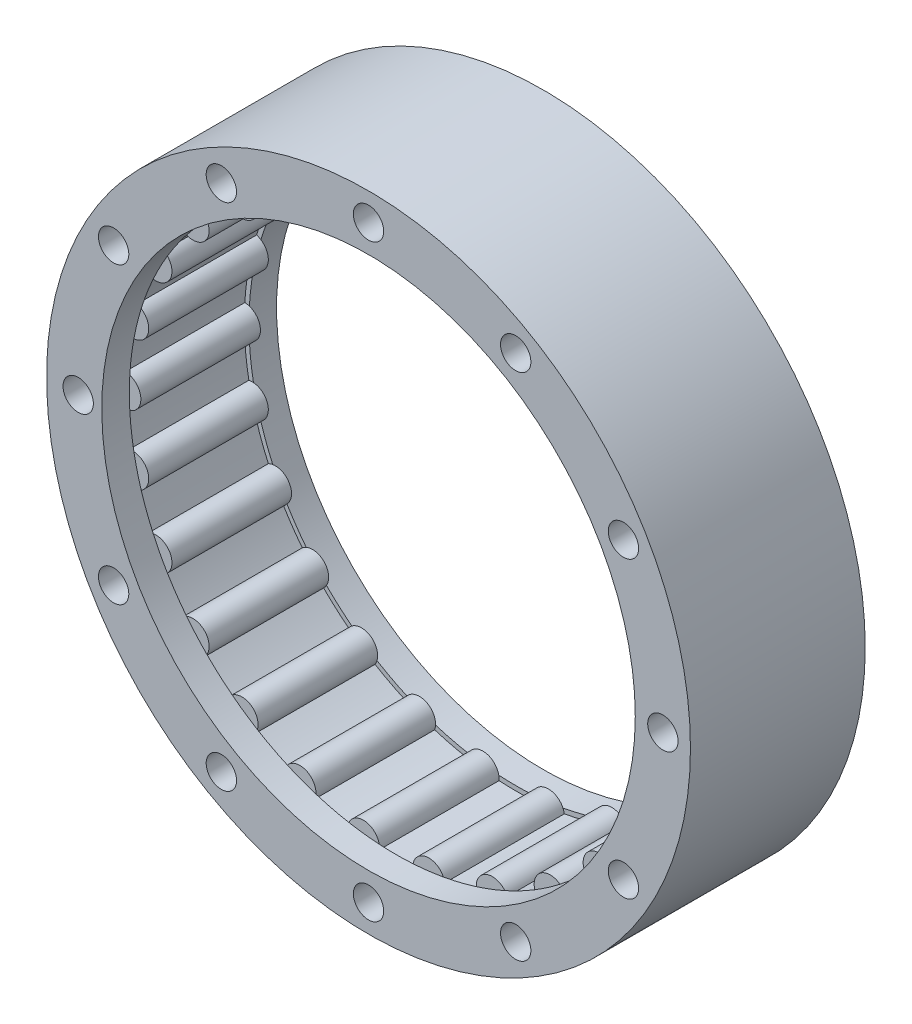
SolidWorks part; units mm, degrees
ref_plane "前视基准面" through (0, 0, 0) normal (0, 0, 1) x (1, 0, 0)
ref_plane "上视基准面" through (0, 0, 0) normal (0, 1, 0) x (1, 0, 0)
ref_plane "右视基准面" through (0, 0, 0) normal (1, 0, 0) x (0, 0, -1)
other "Configuration Table"
sketch "草图1" plane through (0, 0, 0) normal (0, 0, 1) x (1, 0, 0)
  line L0 (0, 0) -> (29.5, 0) construction
  circle A0 centre (0, 0) radius 35
  circle A1 centre (29.5, 0) radius 1.6 construction
  circle A2 centre (0, 0) radius 29.5
  dimension "D1" = 70
  dimension "D2" = 3.2
  dimension "D4" = 59
  dimension "D3" = 29.5
extrude "凸台-拉伸1" add sketch "草图1" along normal blind 13
sketch "草图2" plane through (0, 0, 13) normal (0, 0, 1) x (1, 0, 0)
  circle A0 centre (29.5, 0) radius 1.75
  circle A1 centre (28.6428, -7.0598) radius 1.75
  circle A2 centre (26.121, -13.7093) radius 1.75
  circle A3 centre (22.0811, -19.5621) radius 1.75
  circle A4 centre (16.7579, -24.278) radius 1.75
  circle A5 centre (10.4608, -27.583) radius 1.75
  circle A6 centre (3.5558, -29.2849) radius 1.75
  circle A7 centre (-3.5558, -29.2849) radius 1.75
  circle A8 centre (-10.4608, -27.583) radius 1.75
  circle A9 centre (-16.7579, -24.278) radius 1.75
  circle A10 centre (-22.0811, -19.5621) radius 1.75
  circle A11 centre (-26.121, -13.7093) radius 1.75
  circle A12 centre (-28.6428, -7.0598) radius 1.75
  circle A13 centre (-29.5, 0) radius 1.75
  circle A14 centre (-28.6428, 7.0598) radius 1.75
  circle A15 centre (-26.121, 13.7093) radius 1.75
  circle A16 centre (-22.0811, 19.5621) radius 1.75
  circle A17 centre (-16.7579, 24.278) radius 1.75
  circle A18 centre (-10.4608, 27.583) radius 1.75
  circle A19 centre (-3.5558, 29.2849) radius 1.75
  circle A20 centre (3.5558, 29.2849) radius 1.75
  circle A21 centre (10.4608, 27.583) radius 1.75
  circle A22 centre (16.7579, 24.278) radius 1.75
  circle A23 centre (22.0811, 19.5621) radius 1.75
  circle A24 centre (26.121, 13.7093) radius 1.75
  circle A25 centre (28.6428, 7.0598) radius 1.75
  point P50 (0, 0)
  dimension "D2" = 3.5
  dimension "D1" = 29.5
  dimension "D3" = 26
extrude "凸台-拉伸2" add sketch "草图2" against normal blind 13 separate body
sketch "草图14" plane through (0, 0, 0) normal (0, 0, 1) x (1, 0, 0)
  circle A0 centre (0, 0) radius 35
  circle A1 centre (0, 0) radius 29
extrude "凸台-拉伸3" add sketch "草图14" against normal blind 3
sketch "草图17" plane through (0, 0, 13) normal (0, 0, 1) x (1, 0, 0)
  circle A0 centre (0, 0) radius 29
  circle A2 centre (0, 0) radius 35
extrude "凸台-拉伸4" add sketch "草图17" along normal blind 3
sketch "草图18" plane through (0, 0, -3) normal (0, 0, -1) x (-1, 0, 0)
  line L0 (0, 0) -> (31.5639, 0) construction
  line L1 (0, 0) -> (-32, 0) construction
  line L2 (0, 0) -> (0, -32) construction
  line L3 (0, 0) -> (0, 32) construction
  line L4 (0, 0) -> (27.7128, -16) construction
  line L5 (0, 0) -> (16, -27.7128) construction
  line L6 (0, 0) -> (-16, -27.7128) construction
  line L7 (0, 0) -> (-27.7128, -16) construction
  line L8 (0, 0) -> (-27.7128, 16) construction
  line L9 (0, 0) -> (-16, 27.7128) construction
  line L10 (0, 0) -> (16, 27.7128) construction
  line L11 (0, 0) -> (27.7128, 16) construction
  circle A0 centre (31.5639, 0) radius 1.65
  circle A1 centre (27.7128, -16) radius 1.65
  circle A2 centre (16, -27.7128) radius 1.65
  circle A3 centre (0, -32) radius 1.65
  circle A4 centre (-16, -27.7128) radius 1.65
  circle A5 centre (-27.7128, -16) radius 1.65
  circle A6 centre (-32, 0) radius 1.65
  circle A7 centre (-27.7128, 16) radius 1.65
  circle A8 centre (-16, 27.7128) radius 1.65
  circle A9 centre (0, 32) radius 1.65
  circle A10 centre (16, 27.7128) radius 1.65
  circle A11 centre (27.7128, 16) radius 1.65
  dimension "D1" = 30
  dimension "D2" = 30
  dimension "D3" = 30
  dimension "D4" = 30
  dimension "D5" = 30
  dimension "D6" = 30
  dimension "D7" = 30
  dimension "D8" = 30
extrude "切除-拉伸2" cut sketch "草图18" against normal through all
equation "\"cm\"=1"
